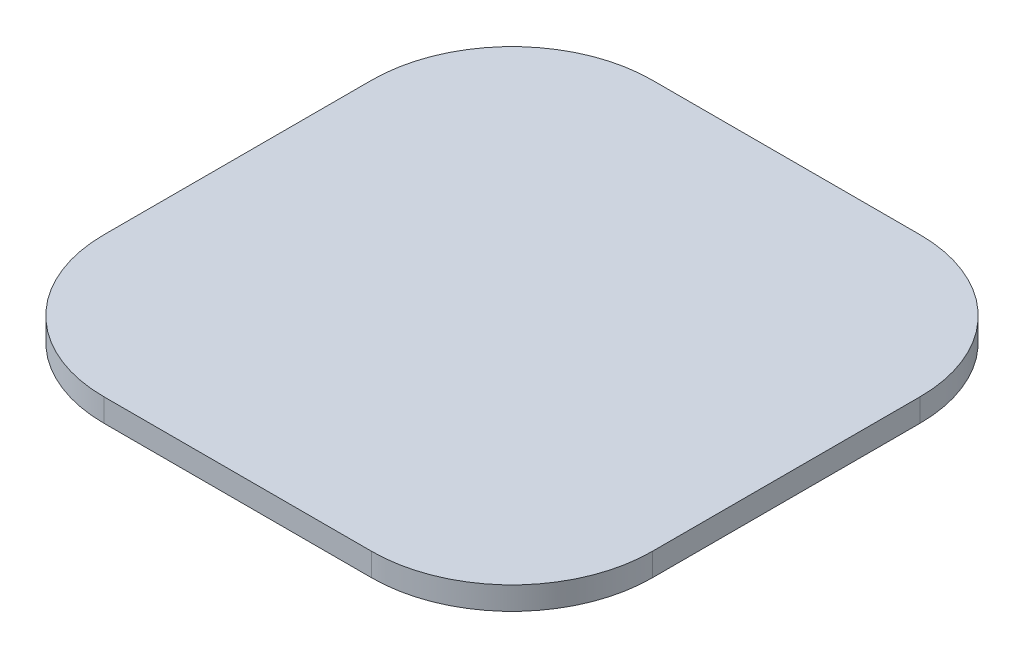
SolidWorks part; units mm, degrees
material "Acrylic (Medium-high impact)"
ref_plane "Front Plane" through (0, 0, 0) normal (0, 0, 1) x (1, 0, 0)
ref_plane "Top Plane" through (0, 0, 0) normal (0, 1, 0) x (1, 0, 0)
ref_plane "Right Plane" through (0, 0, 0) normal (1, 0, 0) x (0, 0, -1)
sketch "Sketch1" plane through (0, 0, 0) normal (0, 1, 0) x (1, 0, 0)
  line L1 (10.5, -21.5) -> (-10.5, -21.5)
  line L2 (21.5, -10.5) -> (21.5, 10.5)
  line L3 (10.5, 21.5) -> (-10.5, 21.5)
  line L4 (-21.5, -10.5) -> (-21.5, 10.5)
  line L5 (21.5, -21.5) -> (-21.5, 21.5) construction
  line L6 (21.5, 21.5) -> (-21.5, -21.5) construction
  arc A0 (-10.5, -21.5) -> (-21.5, -10.5) centre (-10.5, -10.5) cw
  arc A1 (10.5, -21.5) -> (21.5, -10.5) centre (10.5, -10.5) ccw
  arc A2 (21.5, 10.5) -> (10.5, 21.5) centre (10.5, 10.5) ccw
  arc A3 (-10.5, 21.5) -> (-21.5, 10.5) centre (-10.5, 10.5) ccw
  point P0 (0, 0)
  dimension "D3" = 11
  dimension "D1" = 21.5
  dimension "D2" = 21.5
extrude "Boss-Extrude1" add sketch "Sketch1" along normal blind 1.8
